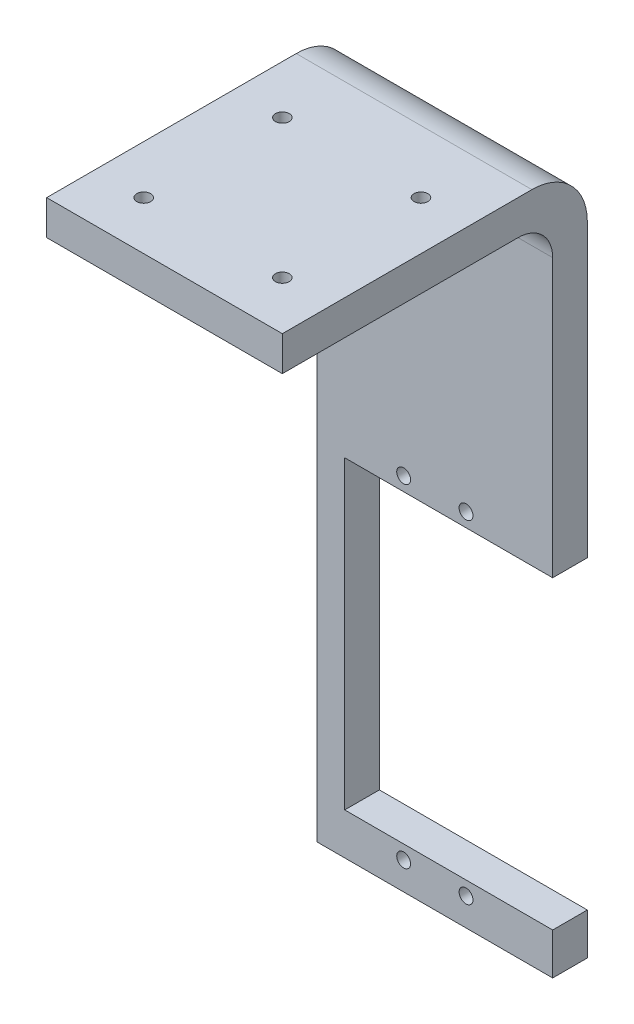
SolidWorks part; units mm, degrees
ref_plane "Front Plane" through (0, 0, 0) normal (0, 0, 1) x (1, 0, 0)
ref_plane "Top Plane" through (0, 0, 0) normal (0, 1, 0) x (1, 0, 0)
ref_plane "Right Plane" through (0, 0, 0) normal (1, 0, 0) x (0, 0, -1)
sketch "Sketch1" plane through (0, 0, 0) normal (0, 0, 1) x (1, 0, 0)
  line L0 (0, 0) -> (0, 24) construction
  line L1 (-17, -28) -> (17, -28)
  line L2 (-17, -28) -> (-17, 67)
  line L3 (-17, 67) -> (17, 67)
  line L4 (17, -28) -> (17, -22)
  line L7 (-13, 22) -> (13, 22)
  line L9 (-13, -22) -> (13, -22)
  line L10 (13, 22) -> (13, 21.4118)
  line L13 (0, 0) -> (17, 0) construction
  line L14 (0, 24) -> (4.5, 24) construction
  line L15 (13, -21.4118) -> (13, -22)
  line L16 (-13, -21.4118) -> (-13, -22)
  line L17 (17, 22) -> (17, 67)
  line L18 (-13, 22) -> (17, 22)
  line L19 (17, -22) -> (-13, -22)
  line L21 (-13, -21.4118) -> (-13, -22)
  line L22 (-13, 22) -> (-13, -22)
  circle A0 centre (4.5, 24) radius 1
  circle A1 centre (-4.5, 24) radius 1
  circle A2 centre (4.5, -24) radius 1
  circle A3 centre (-4.5, -24) radius 1
  point P0 (0, 0)
  point P6 (0, 0)
  dimension "D7" = 6
  dimension "D1" = 45
  dimension "D2" = 34
  dimension "D3" = 26
  dimension "D4" = 44
  dimension "D5" = 24
  dimension "D6" = 4.5
extrude "Boss-Extrude1" add sketch "Sketch1" along normal blind 5
sketch "Sketch2" plane through (0, 67, 0) normal (0, 1, 0) x (1, 0, 0)
  line L0 (-17, -5) -> (17, -5) construction
  line L1 (-17, 0) -> (17, 0)
  line L2 (-17, 0) -> (-17, -44)
  line L3 (-17, -44) -> (17, -44)
  line L4 (17, 0) -> (17, -44)
  line L5 (0, -5) -> (0, -49) construction
  line L6 (0, -27) -> (17, -27) construction
  line L7 (-10, -17) -> (10, -17) construction
  line L8 (-10, -17) -> (-10, -37) construction
  line L9 (-10, -37) -> (10, -37) construction
  line L10 (10, -17) -> (10, -37) construction
  line L11 (-10, -17) -> (10, -37) construction
  line L12 (-10, -37) -> (10, -17) construction
  circle A0 centre (-10, -17) radius 1
  circle A1 centre (10, -17) radius 1
  circle A2 centre (10, -37) radius 1
  circle A3 centre (-10, -37) radius 1
  point P11 (0, -27)
  dimension "D1" = 34
  dimension "D2" = 44
  dimension "D3" = 20
  dimension "D4" = 20
extrude "Boss-Extrude2" add sketch "Sketch2" along normal blind 5
fillet "Fillet1" radius 8 1 edges at (0, 72, 0)
fillet "Fillet3" radius 5 1 edges at (0, 67, 5)
